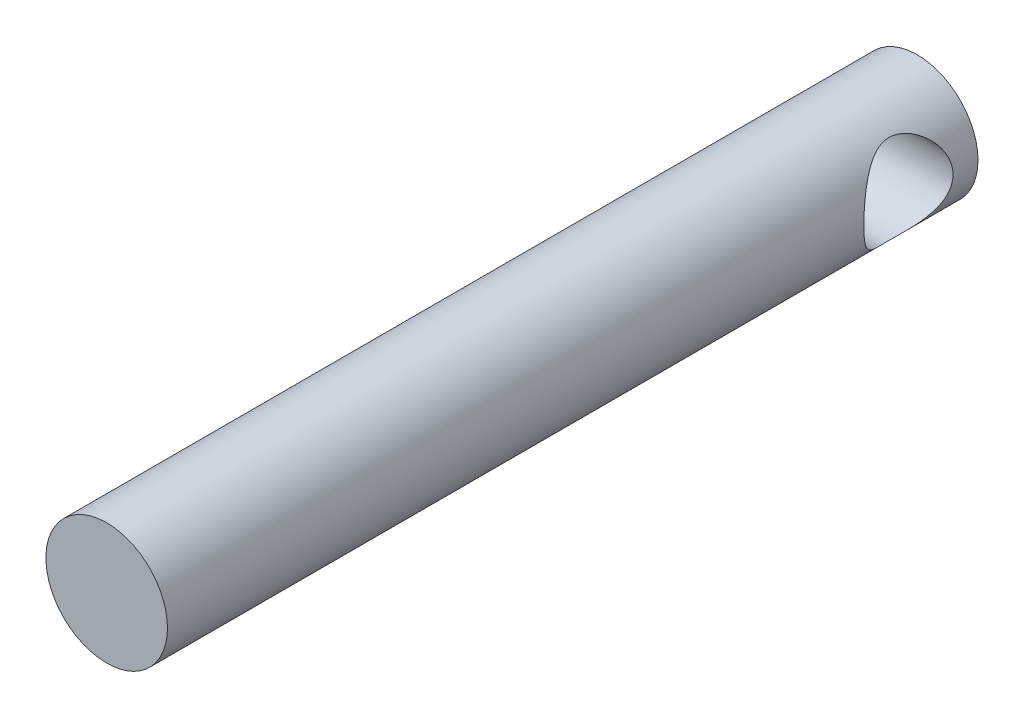
SolidWorks part; units mm, degrees
material "AISI 304"
ref_plane "Front Plane" through (0, 0, 0) normal (0, 0, 1) x (1, 0, 0)
ref_plane "Top Plane" through (0, 0, 0) normal (0, 1, 0) x (1, 0, 0)
ref_plane "Right Plane" through (0, 0, 0) normal (1, 0, 0) x (0, 0, -1)
sketch "Sketch1" plane through (0, 0, 0) normal (0, 0, 1) x (1, 0, 0)
  circle A0 centre (0, 0) radius 7.5
extrude "Boss-Extrude1" add sketch "Sketch1" along normal blind 100
sketch "Sketch2" plane through (0, 0, 0) normal (1, 0, 0) x (0, 0, -1)
  circle A0 centre (-8.586, 0) radius 5.5
extrude "Cut-Extrude1" cut sketch "Sketch2" against normal through all and the other way through all
